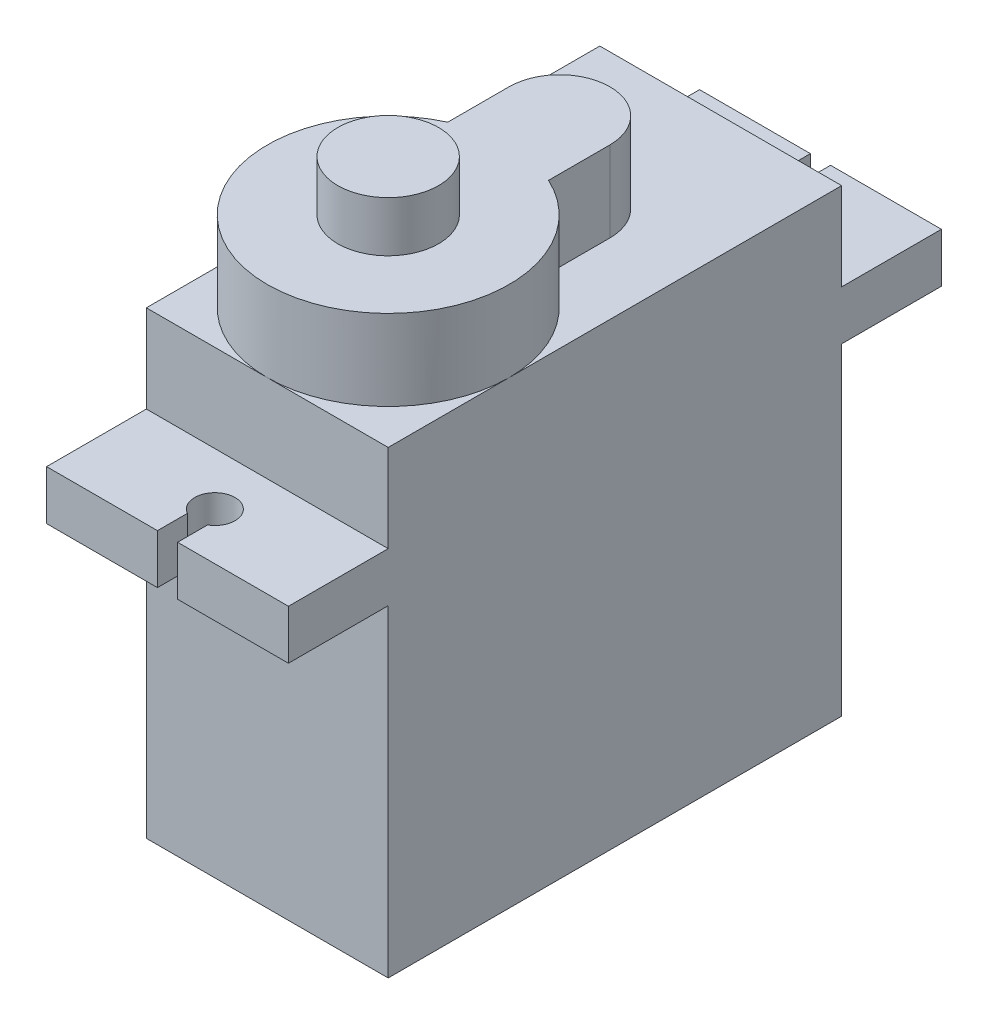
SolidWorks part; units mm, degrees
ref_plane "Front Plane" through (0, 0, 0) normal (0, 0, 1) x (1, 0, 0)
ref_plane "Top Plane" through (0, 0, 0) normal (0, 1, 0) x (1, 0, 0)
ref_plane "Right Plane" through (0, 0, 0) normal (1, 0, 0) x (0, 0, -1)
ref_plane "Plane1"
sketch "Sketch1" plane through (0, 0, 0) normal (1, 0, 0) x (0, 1, 0)
  line L0 (0, 0) -> (0, 11.25)
  line L1 (0, 11.25) -> (16, 11.25)
  line L2 (16, 11.25) -> (16, 16.2)
  line L3 (16, 16.2) -> (18.45, 16.2)
  line L4 (18.45, 16.2) -> (18.45, 11.25)
  line L5 (18.45, 11.25) -> (22.8, 11.25)
  line L6 (22.8, 11.25) -> (22.8, 0)
  line L7 (22.8, 0) -> (22.8, -11.25)
  line L8 (22.8, -11.25) -> (18.45, -11.25)
  line L9 (18.45, -11.25) -> (18.45, -16.2)
  line L10 (18.45, -16.2) -> (16, -16.2)
  line L11 (16, -16.2) -> (16, -11.25)
  line L12 (16, -11.25) -> (0, -11.25)
  line L13 (0, -11.25) -> (0, 0)
  dimension "D1" = 11.25
  dimension "D2" = 2.45
  dimension "D3" = 16
  dimension "D4" = 22.8
extrude "Extrusion1" add sketch "Sketch1" along normal blind 12
sketch "Sketch2" plane through (0, 18.45, 0) normal (0, 1, 0) x (-1, 0, 0)
  line L0 (-6.5, -14.716) -> (-6.5, -16.2)
  line L1 (-6.5, -16.2) -> (-5.5, -16.2)
  line L2 (-5.5, -16.2) -> (-5.5, -14.716)
  line L3 (-6.5, 14.716) -> (-6.5, 16.2)
  line L4 (-6.5, 16.2) -> (-5.5, 16.2)
  line L5 (-5.5, 16.2) -> (-5.5, 14.716)
  arc A0 (-5.5, -14.716) -> (-6.5, -14.716) centre (-6, -13.85) ccw
  arc A1 (-6.5, 14.716) -> (-5.5, 14.716) centre (-6, 13.85) ccw
  dimension "D1" = 2
extrude "Extrusion2" cut sketch "Sketch2" against normal blind 12.6
sketch "Sketch3" plane through (0, 22.8, 0) normal (0, 1, 0) x (-1, 0, 0)
  line L0 (-8.5, -0.2044) -> (-8.5, -3.25)
  line L1 (-3.5, -3.25) -> (-3.5, -0.2044)
  line L2 (0, 11.25) -> (0, 16.2) construction
  arc A0 (-3.5, -0.2044) -> (-8.5, -0.2044) centre (-6, 5.25) ccw
  arc A1 (-8.5, -3.25) -> (-3.5, -3.25) centre (-6, -3.25) ccw
  dimension "D1" = 5
extrude "Extrusion3" add sketch "Sketch3" along normal blind 4
ref_plane "Plane2"
sketch "Sketch4" plane through (0, 26.8, 11.25) normal (0, 1, 0) x (1, 0, 0)
  circle A0 centre (6, 6) radius 2.5
  dimension "D1" = 5
extrude "Extrusion4" add sketch "Sketch4" along normal blind 2.5
